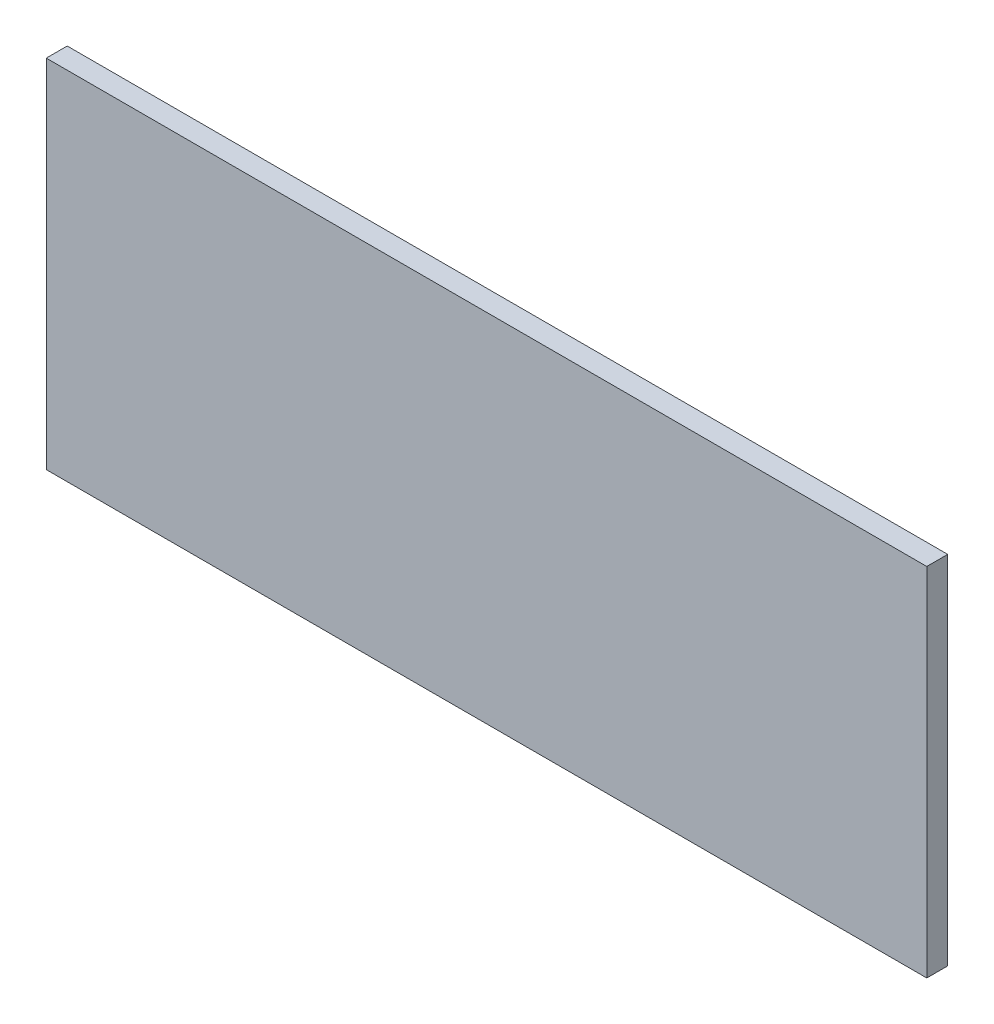
SolidWorks part; units mm, degrees
ref_plane "Front Plane" through (0, 0, 0) normal (0, 0, 1) x (1, 0, 0)
ref_plane "Top Plane" through (0, 0, 0) normal (0, 1, 0) x (1, 0, 0)
ref_plane "Right Plane" through (0, 0, 0) normal (1, 0, 0) x (0, 0, -1)
sketch "Sketch1" plane through (0, 0, 0) normal (0, 0, 1) x (1, 0, 0)
  line L1 (0, 0) -> (210, 0)
  line L2 (0, 0) -> (0, 85)
  line L3 (0, 85) -> (210, 85)
  line L4 (210, 0) -> (210, 85)
  dimension "D1" = 210
  dimension "D2" = 85
extrude "Boss-Extrude1" add sketch "Sketch1" along normal blind 5
